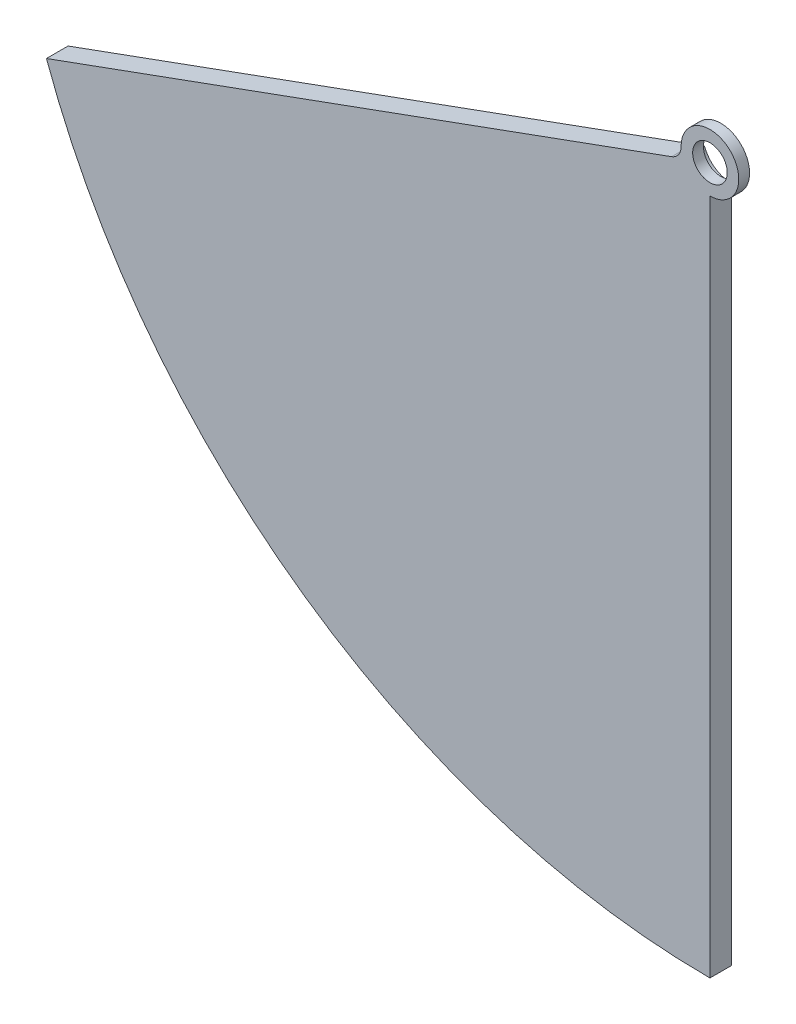
SolidWorks part; units mm, degrees
ref_plane "Płaszczyzna przednia" through (0, 0, 0) normal (0, 0, 1) x (1, 0, 0)
ref_plane "Płaszczyzna górna" through (0, 0, 0) normal (0, 1, 0) x (1, 0, 0)
ref_plane "Płaszczyzna prawa" through (0, 0, 0) normal (1, 0, 0) x (0, 0, -1)
sketch "Szkic1" plane through (0, 0, 0) normal (0, 0, 1) x (1, 0, 0)
  line L0 (0, -20) -> (0, -490)
  line L1 (-18.7939, -6.8404) -> (-460.4494, -167.5899)
  arc A0 (-460.4494, -167.5899) -> (0, -490) centre (0, 0) ccw
  circle A1 centre (0, 0) radius 12
  arc A2 (0, -20) -> (-18.7939, -6.8404) centre (0, 0) ccw
  dimension "D2" = 490
  dimension "D3" = 24
  dimension "D4" = 20
  dimension "D1" = 70
extrude "Dodanie-wyciągnięcie1" add sketch "Szkic1" along normal blind 15
sketch "Szkic2" plane through (0, 0, 0) normal (0, 0, -1) x (-1, 0, 0)
  circle A0 centre (0, 0) radius 20
  dimension "D1" = 40
extrude "Wytnij-wyciągnięcie1" cut sketch "Szkic2" against normal blind 7.5
fillet "Zaokrąglenie1" radius 10 1 edges at (-18.7939, -6.8404, 11.25)
